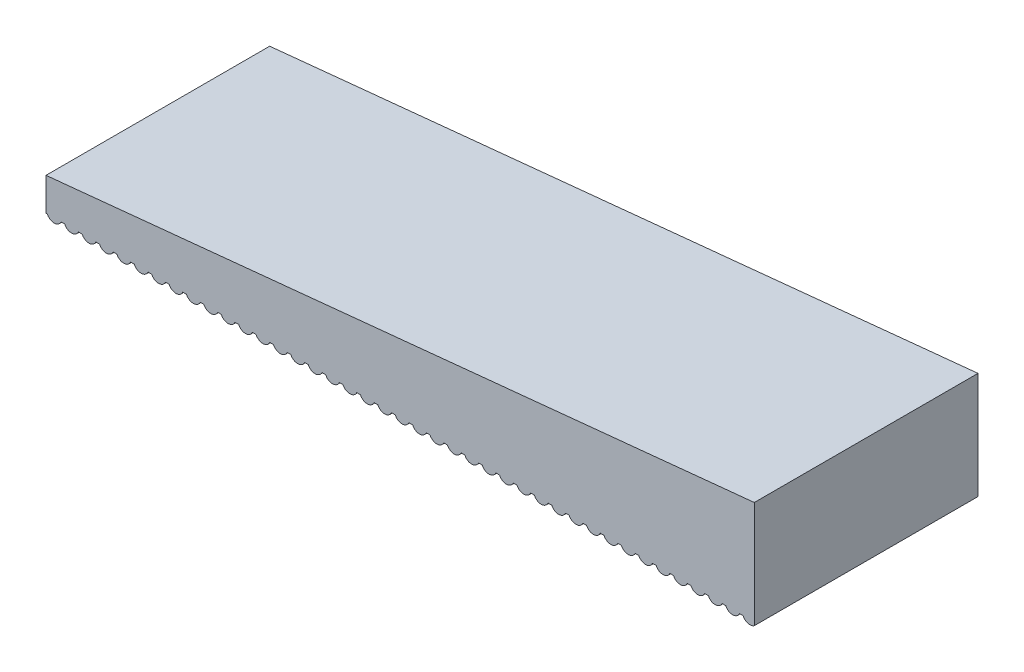
SolidWorks part; units mm, degrees
material "Silicon"
ref_plane "Front" through (0, 0, 0) normal (0, 0, 1) x (1, 0, 0)
ref_plane "Top" through (0, 0, 0) normal (0, 1, 0) x (1, 0, 0)
ref_plane "Right" through (0, 0, 0) normal (1, 0, 0) x (0, 0, -1)
sketch "Sketch1" plane through (0, 0, 0) normal (0, 0, 1) x (1, 0, 0)
  line L0 (0, 0) -> (10, 1) construction
  line L1 (10, 1) -> (10, 0) construction
  line L2 (10, 0) -> (0, 0) construction
  line L3 (0, 0) -> (10, 1)
  line L4 (10, 1) -> (10, -0.5)
  line L5 (10, -0.5) -> (0, -0.5)
  line L6 (0, -0.5) -> (0, 0)
  dimension "D1" = 1
  dimension "D2" = 10
  dimension "D3" = 0.5
extrude "Boss-Extrude1" add sketch "Sketch1" along normal mid plane 3
sketch "Sketch2" plane through (0, 0, 1.5) normal (0, 0, 1) x (1, 0, 0)
  line L1 (0, -0.5) -> (10, -0.5) construction
  line L2 (9.8167, -0.44) -> (9.7667, -0.44)
  line L3 (9.7667, -0.44) -> (9.7667, -0.5) construction
  line L4 (10, 1) -> (0, 0) construction
  line L5 (9.5834, -0.44) -> (9.5334, -0.44)
  line L6 (9.5334, -0.44) -> (9.5334, -0.5) construction
  line L7 (9.3501, -0.44) -> (9.3001, -0.44)
  line L8 (9.3001, -0.44) -> (9.3001, -0.5) construction
  line L9 (9.1168, -0.44) -> (9.0668, -0.44)
  line L10 (9.0668, -0.44) -> (9.0668, -0.5) construction
  line L11 (8.8835, -0.44) -> (8.8335, -0.44)
  line L12 (8.8335, -0.44) -> (8.8335, -0.5) construction
  line L13 (8.6502, -0.44) -> (8.6002, -0.44)
  line L14 (8.6002, -0.44) -> (8.6002, -0.5) construction
  line L15 (8.4169, -0.44) -> (8.3669, -0.44)
  line L16 (8.3669, -0.44) -> (8.3669, -0.5) construction
  line L17 (8.1836, -0.44) -> (8.1336, -0.44)
  line L18 (8.1336, -0.44) -> (8.1336, -0.5) construction
  line L19 (7.9503, -0.44) -> (7.9003, -0.44)
  line L20 (7.9003, -0.44) -> (7.9003, -0.5) construction
  line L21 (7.717, -0.44) -> (7.667, -0.44)
  line L22 (7.667, -0.44) -> (7.667, -0.5) construction
  line L23 (7.4837, -0.44) -> (7.4337, -0.44)
  line L24 (7.4337, -0.44) -> (7.4337, -0.5) construction
  line L25 (7.2504, -0.44) -> (7.2004, -0.44)
  line L26 (7.2004, -0.44) -> (7.2004, -0.5) construction
  line L27 (7.0171, -0.44) -> (6.9671, -0.44)
  line L28 (6.9671, -0.44) -> (6.9671, -0.5) construction
  line L29 (6.7838, -0.44) -> (6.7338, -0.44)
  line L30 (6.7338, -0.44) -> (6.7338, -0.5) construction
  line L31 (6.5505, -0.44) -> (6.5005, -0.44)
  line L32 (6.5005, -0.44) -> (6.5005, -0.5) construction
  line L33 (6.3172, -0.44) -> (6.2672, -0.44)
  line L34 (6.2672, -0.44) -> (6.2672, -0.5) construction
  line L35 (6.0838, -0.44) -> (6.0338, -0.44)
  line L36 (6.0338, -0.44) -> (6.0338, -0.5) construction
  line L37 (5.8505, -0.44) -> (5.8005, -0.44)
  line L38 (5.8005, -0.44) -> (5.8005, -0.5) construction
  line L39 (5.6172, -0.44) -> (5.5672, -0.44)
  line L40 (5.5672, -0.44) -> (5.5672, -0.5) construction
  line L41 (5.3839, -0.44) -> (5.3339, -0.44)
  line L42 (5.3339, -0.44) -> (5.3339, -0.5) construction
  line L43 (5.1506, -0.44) -> (5.1006, -0.44)
  line L44 (5.1006, -0.44) -> (5.1006, -0.5) construction
  line L45 (4.9173, -0.44) -> (4.8673, -0.44)
  line L46 (4.8673, -0.44) -> (4.8673, -0.5) construction
  line L47 (4.684, -0.44) -> (4.634, -0.44)
  line L48 (4.634, -0.44) -> (4.634, -0.5) construction
  line L49 (4.4507, -0.44) -> (4.4007, -0.44)
  line L50 (4.4007, -0.44) -> (4.4007, -0.5) construction
  line L51 (4.2174, -0.44) -> (4.1674, -0.44)
  line L52 (4.1674, -0.44) -> (4.1674, -0.5) construction
  line L53 (3.9841, -0.44) -> (3.9341, -0.44)
  line L54 (3.9341, -0.44) -> (3.9341, -0.5) construction
  line L55 (3.7508, -0.44) -> (3.7008, -0.44)
  line L56 (3.7008, -0.44) -> (3.7008, -0.5) construction
  line L57 (3.5175, -0.44) -> (3.4675, -0.44)
  line L58 (3.4675, -0.44) -> (3.4675, -0.5) construction
  line L59 (3.2842, -0.44) -> (3.2342, -0.44)
  line L60 (3.2342, -0.44) -> (3.2342, -0.5) construction
  line L61 (3.0509, -0.44) -> (3.0009, -0.44)
  line L62 (3.0009, -0.44) -> (3.0009, -0.5) construction
  line L63 (2.8176, -0.44) -> (2.7676, -0.44)
  line L64 (2.7676, -0.44) -> (2.7676, -0.5) construction
  line L65 (2.5843, -0.44) -> (2.5343, -0.44)
  line L66 (2.5343, -0.44) -> (2.5343, -0.5) construction
  line L67 (2.351, -0.44) -> (2.301, -0.44)
  line L68 (2.301, -0.44) -> (2.301, -0.5) construction
  line L69 (2.1177, -0.44) -> (2.0677, -0.44)
  line L70 (2.0677, -0.44) -> (2.0677, -0.5) construction
  line L71 (1.8844, -0.44) -> (1.8344, -0.44)
  line L72 (1.8344, -0.44) -> (1.8344, -0.5) construction
  line L73 (1.6511, -0.44) -> (1.6011, -0.44)
  line L74 (1.6011, -0.44) -> (1.6011, -0.5) construction
  line L75 (1.4178, -0.44) -> (1.3678, -0.44)
  line L76 (1.3678, -0.44) -> (1.3678, -0.5) construction
  line L77 (1.1845, -0.44) -> (1.1345, -0.44)
  line L78 (10, -0.44) -> (10, 1)
  line L79 (10, -0.5) -> (10, 1) construction
  line L80 (1.1345, -0.44) -> (1.1345, -0.5) construction
  line L81 (0.9512, -0.44) -> (0.9012, -0.44)
  line L83 (0.9012, -0.44) -> (0.9012, -0.5) construction
  line L84 (0.7179, -0.44) -> (0.6679, -0.44)
  line L85 (0.6679, -0.44) -> (0.6679, -0.5) construction
  line L86 (0.4846, -0.44) -> (0.4346, -0.44)
  line L87 (0.4346, -0.44) -> (0.4346, -0.5) construction
  line L88 (0.2513, -0.44) -> (0.2013, -0.44)
  line L89 (0.2013, -0.44) -> (0.2013, -0.5) construction
  line L90 (0.018, -0.44) -> (0, -0.44)
  line L96 (0, 0) -> (0, -0.5) construction
  line L97 (0, 0) -> (0, -0.44)
  line L99 (10, 1) -> (0, 0)
  line L162 (-0.2153, -0.44) -> (-0.2653, -0.44) [skipped]
  line L163 (-0.4486, -0.44) -> (-0.4986, -0.44) [skipped]
  line L164 (-0.032, -0.44) -> (-0.032, -0.5) construction
  line L165 (-0.2653, -0.44) -> (-0.2653, -0.5) construction
  line L166 (-0.4986, -0.44) -> (-0.4986, -0.5) construction
  arc A0 (10, -0.44) -> (9.8167, -0.44) centre (9.9083, -0.4) cw
  arc A1 (9.7667, -0.44) -> (9.5834, -0.44) centre (9.675, -0.4) cw
  arc A2 (9.5334, -0.44) -> (9.3501, -0.44) centre (9.4417, -0.4) cw
  arc A3 (9.3001, -0.44) -> (9.1168, -0.44) centre (9.2084, -0.4) cw
  arc A4 (9.0668, -0.44) -> (8.8835, -0.44) centre (8.9751, -0.4) cw
  arc A5 (8.8335, -0.44) -> (8.6502, -0.44) centre (8.7418, -0.4) cw
  arc A6 (8.6002, -0.44) -> (8.4169, -0.44) centre (8.5085, -0.4) cw
  arc A7 (8.3669, -0.44) -> (8.1836, -0.44) centre (8.2752, -0.4) cw
  arc A8 (8.1336, -0.44) -> (7.9503, -0.44) centre (8.0419, -0.4) cw
  arc A9 (7.9003, -0.44) -> (7.717, -0.44) centre (7.8086, -0.4) cw
  arc A10 (7.667, -0.44) -> (7.4837, -0.44) centre (7.5753, -0.4) cw
  arc A11 (7.4337, -0.44) -> (7.2504, -0.44) centre (7.342, -0.4) cw
  arc A12 (7.2004, -0.44) -> (7.0171, -0.44) centre (7.1087, -0.4) cw
  arc A13 (6.9671, -0.44) -> (6.7838, -0.44) centre (6.8754, -0.4) cw
  arc A14 (6.7338, -0.44) -> (6.5505, -0.44) centre (6.6421, -0.4) cw
  arc A15 (6.5005, -0.44) -> (6.3172, -0.44) centre (6.4088, -0.4) cw
  arc A16 (6.2672, -0.44) -> (6.0838, -0.44) centre (6.1755, -0.4) cw
  arc A17 (6.0338, -0.44) -> (5.8505, -0.44) centre (5.9422, -0.4) cw
  arc A18 (5.8005, -0.44) -> (5.6172, -0.44) centre (5.7089, -0.4) cw
  arc A19 (5.5672, -0.44) -> (5.3839, -0.44) centre (5.4756, -0.4) cw
  arc A20 (5.3339, -0.44) -> (5.1506, -0.44) centre (5.2423, -0.4) cw
  arc A21 (5.1006, -0.44) -> (4.9173, -0.44) centre (5.009, -0.4) cw
  arc A22 (4.8673, -0.44) -> (4.684, -0.44) centre (4.7757, -0.4) cw
  arc A23 (4.634, -0.44) -> (4.4507, -0.44) centre (4.5424, -0.4) cw
  arc A24 (4.4007, -0.44) -> (4.2174, -0.44) centre (4.3091, -0.4) cw
  arc A25 (4.1674, -0.44) -> (3.9841, -0.44) centre (4.0758, -0.4) cw
  arc A26 (3.9341, -0.44) -> (3.7508, -0.44) centre (3.8425, -0.4) cw
  arc A27 (3.7008, -0.44) -> (3.5175, -0.44) centre (3.6092, -0.4) cw
  arc A28 (3.4675, -0.44) -> (3.2842, -0.44) centre (3.3759, -0.4) cw
  arc A29 (3.2342, -0.44) -> (3.0509, -0.44) centre (3.1426, -0.4) cw
  arc A30 (3.0009, -0.44) -> (2.8176, -0.44) centre (2.9093, -0.4) cw
  arc A31 (2.7676, -0.44) -> (2.5843, -0.44) centre (2.676, -0.4) cw
  arc A32 (2.5343, -0.44) -> (2.351, -0.44) centre (2.4427, -0.4) cw
  arc A33 (2.301, -0.44) -> (2.1177, -0.44) centre (2.2093, -0.4) cw
  arc A34 (2.0677, -0.44) -> (1.8844, -0.44) centre (1.976, -0.4) cw
  arc A35 (1.8344, -0.44) -> (1.6511, -0.44) centre (1.7427, -0.4) cw
  arc A36 (1.6011, -0.44) -> (1.4178, -0.44) centre (1.5094, -0.4) cw
  arc A37 (1.3678, -0.44) -> (1.1845, -0.44) centre (1.2761, -0.4) cw
  arc A38 (1.1345, -0.44) -> (0.9512, -0.44) centre (1.0428, -0.4) cw
  arc A39 (0.9012, -0.44) -> (0.7179, -0.44) centre (0.8095, -0.4) cw
  arc A40 (0.6679, -0.44) -> (0.4846, -0.44) centre (0.5762, -0.4) cw
  arc A41 (0.4346, -0.44) -> (0.2513, -0.44) centre (0.3429, -0.4) cw
  arc A42 (0.2013, -0.44) -> (0.018, -0.44) centre (0.1096, -0.4) cw
  arc A79 (-0.032, -0.44) -> (-0.2153, -0.44) centre (-0.1237, -0.4) cw [skipped]
  arc A80 (-0.2653, -0.44) -> (-0.4486, -0.44) centre (-0.357, -0.4) cw [skipped]
  point P6 (9.9083, -0.5)
  dimension "D1" = 0.1
  dimension "D2" = 0.06
  dimension "D3" = 0.05
  dimension "D4" = 45
extrude "Cut-Extrude1" cut sketch "Sketch2" against normal through all both and the other way through all flip side to cut
sketch "Sketch4" plane through (10, 0, 0) normal (1, 0, 0) x (0, 0, -1)
  line L1 (1.5, -0.5) -> (1.5, -0.44) construction
  line L2 (-1.5, -0.44) -> (-1.5, -0.5) construction
  line L3 (1.5, -0.44) -> (1.5, 1) construction
  line L4 (1.5, 1) -> (-1.5, 1) construction
  line L5 (-1.5, 1) -> (-1.5, -0.44) construction
  line L6 (-1.5, -0.5) -> (1.5, -0.5)
  line L7 (1.5, -0.5) -> (1.5, -0.44)
  line L8 (-1.5, -0.44) -> (-1.5, -0.5)
  line L9 (1.5, -0.44) -> (1.5, 1)
  line L10 (1.5, 1) -> (-1.5, 1)
  line L11 (-1.5, 1) -> (-1.5, -0.44)
extrude "Cut-Extrude2" cut sketch "Sketch4" against normal blind 0.5
